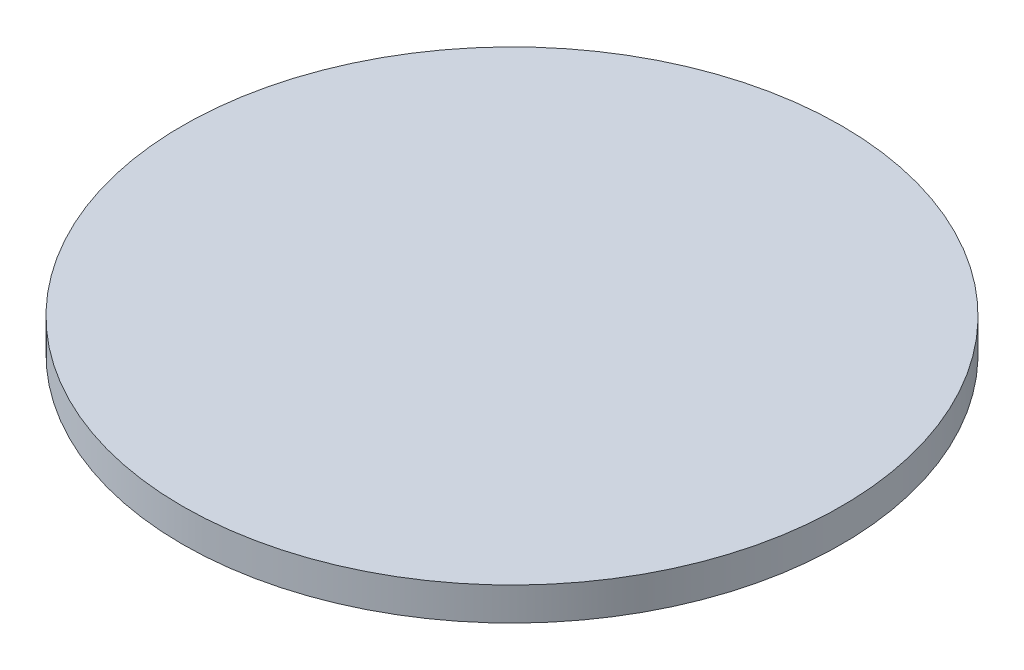
SolidWorks part; units mm, degrees
ref_plane "前视基准面" through (0, 0, 0) normal (0, 0, 1) x (1, 0, 0)
ref_plane "上视基准面" through (0, 0, 0) normal (0, 1, 0) x (1, 0, 0)
ref_plane "右视基准面" through (0, 0, 0) normal (1, 0, 0) x (0, 0, -1)
sketch "草图1" plane through (0, 0, 0) normal (0, 1, 0) x (1, 0, 0)
  circle A0 centre (0, 0) radius 12.5
  dimension "D1" = 25
extrude "凸台-拉伸1" add sketch "草图1" along normal blind 1.25
